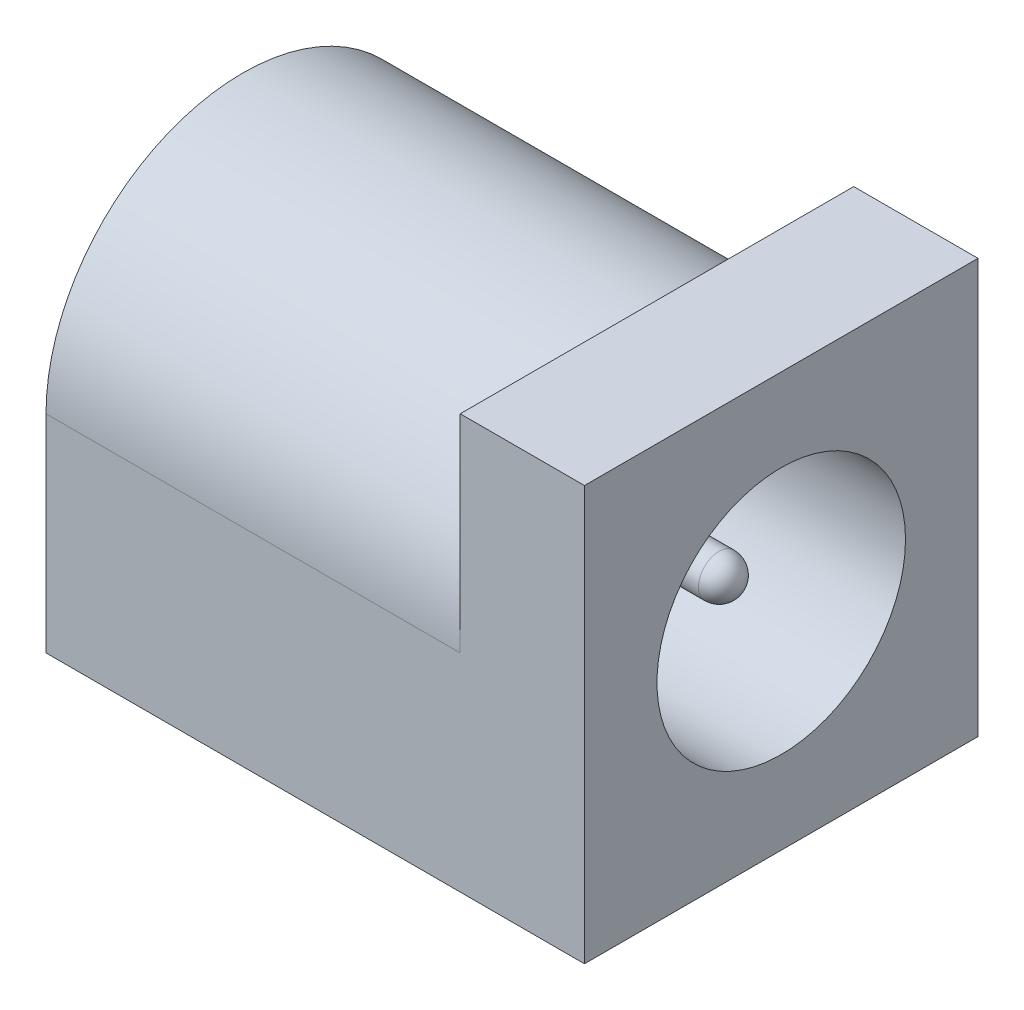
SolidWorks part; units mm, degrees
ref_plane "Front Plane" through (0, 0, 0) normal (0, 0, 1) x (1, 0, 0)
ref_plane "Top Plane" through (0, 0, 0) normal (0, 1, 0) x (1, 0, 0)
ref_plane "Right Plane" through (0, 0, 0) normal (1, 0, 0) x (0, 0, -1)
sketch "Sketch1" plane through (0, 0, 0) normal (1, 0, 0) x (0, 0, -1)
  line L1 (-4.75, -2.5) -> (4.75, -2.5)
  line L2 (-4.75, -2.5) -> (-4.75, 2.5)
  line L4 (4.75, -2.5) -> (4.75, 2.5)
  line L5 (-4.75, -2.5) -> (4.75, 2.5) construction
  line L6 (-4.75, 2.5) -> (4.75, -2.5) construction
  arc A0 (-4.75, 2.5) -> (4.75, 2.5) centre (0, 2.5) cw
  point P0 (0, 0)
  dimension "D3" = 4.75
  dimension "D1" = 9.5
  dimension "D2" = 5
extrude "Boss-Extrude1" add sketch "Sketch1" along normal blind 10
sketch "Sketch2" plane through (10, 0, 0) normal (1, 0, 0) x (0, 0, -1)
  line L5 (-4.75, -2.5) -> (4.75, -2.5) construction
  line L6 (-4.75, 7.5) -> (4.75, 7.5)
  line L8 (-4.75, 7.5) -> (-4.75, -2.5)
  line L9 (-4.75, -2.5) -> (4.75, -2.5)
  line L10 (4.75, 7.5) -> (4.75, -2.5)
  dimension "D1" = 9.5
  dimension "D2" = 4.75
  dimension "D3" = 10
extrude "Boss-Extrude2" add sketch "Sketch2" along normal blind 3
sketch "Sketch3" plane through (13, 0, 0) normal (1, 0, 0) x (0, 0, -1)
  circle A0 centre (0, 2.5) radius 3
  arc A1 (4.75, 2.5) -> (-4.75, 2.5) centre (0, 2.5) ccw construction
  dimension "D1" = 6
extrude "Cut-Extrude1" cut sketch "Sketch3" against normal blind 12
sketch "Sketch4" plane through (1, 0, 0) normal (1, 0, 0) x (0, 0, -1)
  circle A0 centre (0, 2.5) radius 0.5
  dimension "D1" = 1
extrude "Boss-Extrude3" add sketch "Sketch4" along normal blind 11
fillet "Fillet1" radius 0.5 1 edges at (12, 2.5, -0.5)
